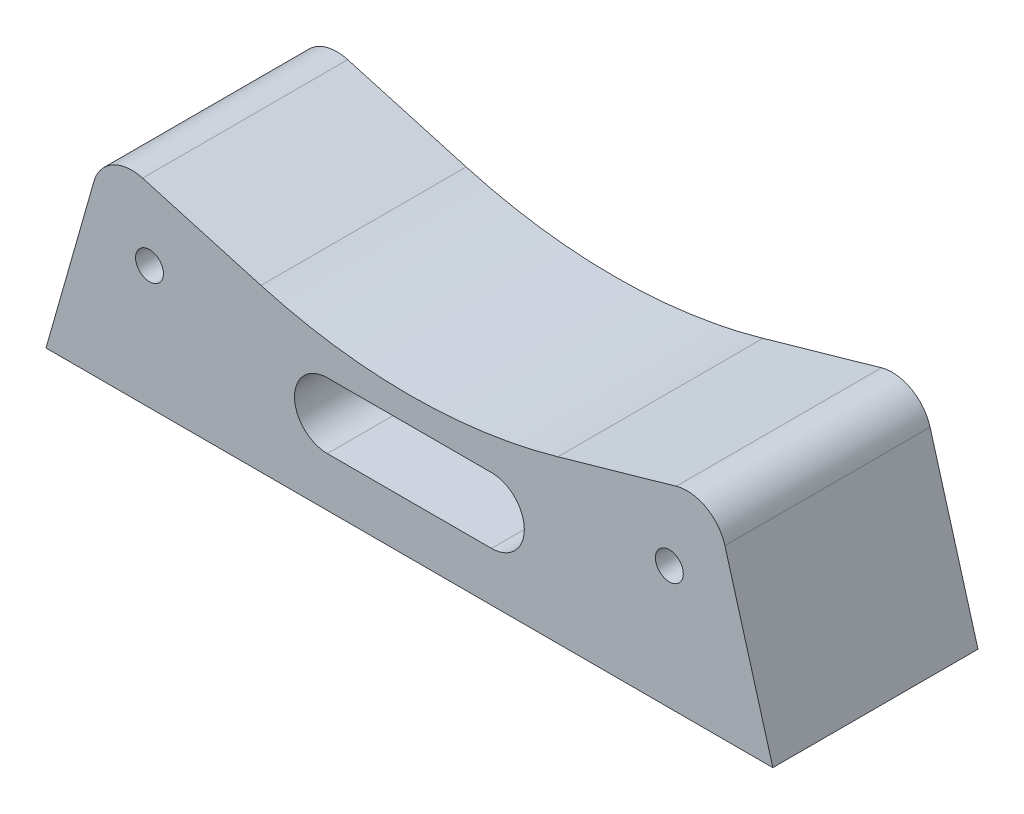
SolidWorks part; units mm, degrees
ref_plane "Plan de face" through (0, 0, 0) normal (0, 0, 1) x (1, 0, 0)
ref_plane "Plan de dessus" through (0, 0, 0) normal (0, 1, 0) x (1, 0, 0)
ref_plane "Plan de droite" through (0, 0, 0) normal (1, 0, 0) x (0, 0, -1)
sketch "Esquisse1" plane through (0, 0, 25) normal (0, 0, 1) x (1, 0, 0)
  line L2 (18.0308, -30.0994) -> (32.4578, -25.9931) construction
  line L3 (38.6356, -29.4333) -> (45.2425, -52.646) construction
  line L4 (0, 33.25) -> (0, -123.7733) construction
  line L5 (0, 33.25) -> (0, -123.7733) construction
  line L6 (18.0856, -30.2918) -> (32.5126, -26.1855)
  line L7 (38.4432, -29.4881) -> (44.2814, -50)
  line L8 (-44.2814, -50) -> (44.2814, -50)
  line L9 (35, 0) -> (-35, 0) construction
  line L10 (38.4432, -29.4881) -> (45.0501, -52.7007) construction
  line L11 (-38.6356, -29.4333) -> (-45.2425, -52.646) construction
  line L12 (-18.0308, -30.0994) -> (-32.4578, -25.9931) construction
  line L13 (-38.4432, -29.4881) -> (-44.2814, -50)
  line L14 (-18.0856, -30.2918) -> (-32.5126, -26.1855)
  arc A2 (0, -32.6154) -> (18.0308, -30.0994) centre (0, 33.25) ccw construction
  arc A3 (38.6356, -29.4333) -> (32.4578, -25.9931) centre (33.8266, -30.8021) ccw construction
  arc A5 (0, -32.8154) -> (18.0856, -30.2918) centre (0, 33.25) ccw
  arc A6 (38.4432, -29.4881) -> (32.5126, -26.1855) centre (33.8266, -30.8021) ccw
  arc A7 (-38.6356, -29.4333) -> (-32.4578, -25.9931) centre (-33.8266, -30.8021) cw construction
  arc A8 (0, -32.6154) -> (-18.0308, -30.0994) centre (0, 33.25) cw construction
  arc A9 (-38.4432, -29.4881) -> (-32.5126, -26.1855) centre (-33.8266, -30.8021) cw
  arc A10 (0, -32.8154) -> (-18.0856, -30.2918) centre (0, 33.25) cw
  point P3 (0, -32.6154)
  point P34 (0, -50)
  dimension "D2" = 50
  dimension "D1" = 0.2
extrude "Boss.-Extru.1" add sketch "Esquisse1" against normal up to surface (25 mm away)
sketch "Esquisse2" plane through (0, 0, 0) normal (0, 0, -1) x (-1, 0, 0)
  line L0 (10, -36) -> (-10, -36) construction
  line L1 (10, -36) -> (-10, -36)
  line L2 (-10, -44) -> (10, -44) construction
  line L3 (-10, -44) -> (10, -44)
  line L5 (44.2814, -50) -> (38.4432, -29.4881)
  line L6 (32.5126, -26.1855) -> (18.0856, -30.2918)
  line L7 (-18.0856, -30.2918) -> (-32.5126, -26.1855)
  line L8 (-38.4432, -29.4881) -> (-44.2814, -50)
  line L9 (-44.2814, -50) -> (44.2814, -50)
  line L10 (44.2814, -50) -> (38.4432, -29.4881)
  line L11 (32.5126, -26.1855) -> (18.0856, -30.2918)
  line L12 (-18.0856, -30.2918) -> (-32.5126, -26.1855)
  line L13 (-38.4432, -29.4881) -> (-44.2814, -50)
  line L14 (-44.2814, -50) -> (44.2814, -50)
  arc A0 (-10, -36) -> (-10, -44) centre (-10, -40) ccw construction
  arc A1 (10, -44) -> (10, -36) centre (10, -40) ccw construction
  arc A2 (-10, -36) -> (-10, -44) centre (-10, -40) ccw
  arc A3 (38.4432, -29.4881) -> (32.5126, -26.1855) centre (33.8266, -30.8021) ccw
  arc A4 (-18.0856, -30.2918) -> (18.0856, -30.2918) centre (0, 33.25) ccw
  arc A5 (-32.5126, -26.1855) -> (-38.4432, -29.4881) centre (-33.8266, -30.8021) ccw
  arc A6 (38.4432, -29.4881) -> (32.5126, -26.1855) centre (33.8266, -30.8021) ccw
  arc A7 (-18.0856, -30.2918) -> (18.0856, -30.2918) centre (0, 33.25) ccw
  arc A8 (-32.5126, -26.1855) -> (-38.4432, -29.4881) centre (-33.8266, -30.8021) ccw
  arc A9 (10, -44) -> (10, -36) centre (10, -40) ccw
  dimension "D1" = 0
extrude "Enlèv. mat.-Extru.1" cut sketch "Esquisse2" against normal through all contours L3 A9 L1 A2
sketch "Esquisse13" plane through (0, 0, -3) normal (0, 0, -1) x (-1, 0, 0)
  circle A0 centre (31.67, -35) radius 1.7 construction
  circle A1 centre (-31.67, -35) radius 1.7 construction
  circle A2 centre (31.67, -35) radius 1.7
  circle A3 centre (-31.67, -35) radius 1.7
extrude "Enlèv. mat.-Extru.2" cut sketch "Esquisse13" against normal through all
